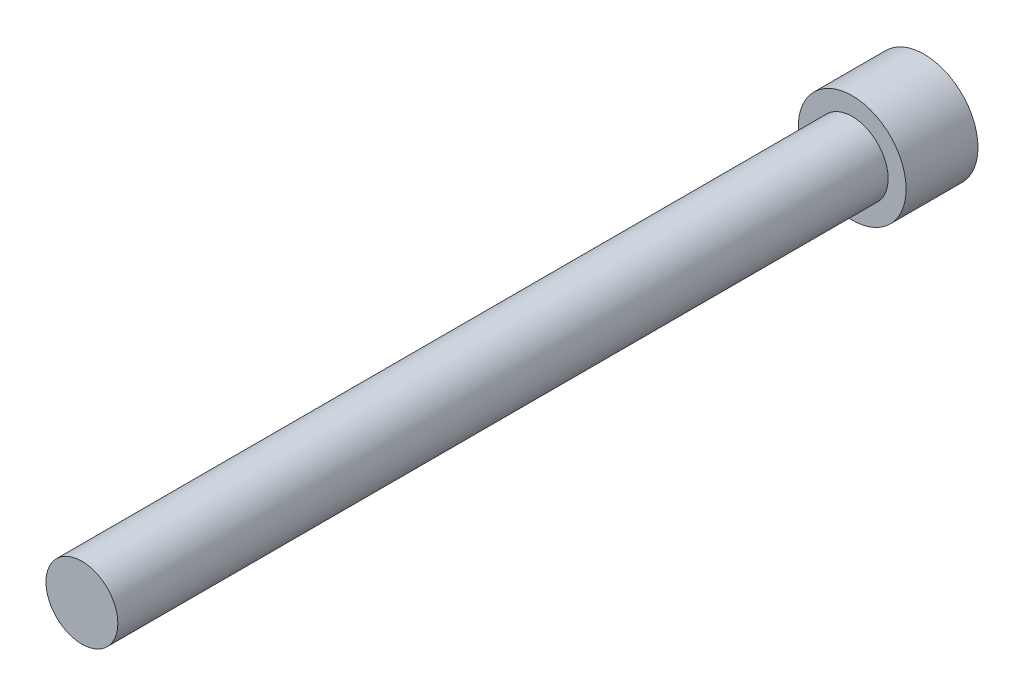
SolidWorks part; units mm, degrees
ref_plane "前视基准面" through (0, 0, 0) normal (0, 0, 1) x (1, 0, 0)
ref_plane "上视基准面" through (0, 0, 0) normal (0, 1, 0) x (1, 0, 0)
ref_plane "右视基准面" through (0, 0, 0) normal (1, 0, 0) x (0, 0, -1)
sketch "草图1" plane through (0, 0, 0) normal (0, 0, 1) x (1, 0, 0)
  circle A0 centre (-16.4105, 16.545) radius 10.5
extrude "凸台-拉伸1" add sketch "草图1" along normal blind 14
ref_point "点1"
sketch "草图2" plane through (0, 0, 14) normal (0, 0, 1) x (1, 0, 0)
  circle A0 centre (-16.4105, 16.545) radius 7
extrude "凸台-拉伸2" add sketch "草图2" along normal blind 150
